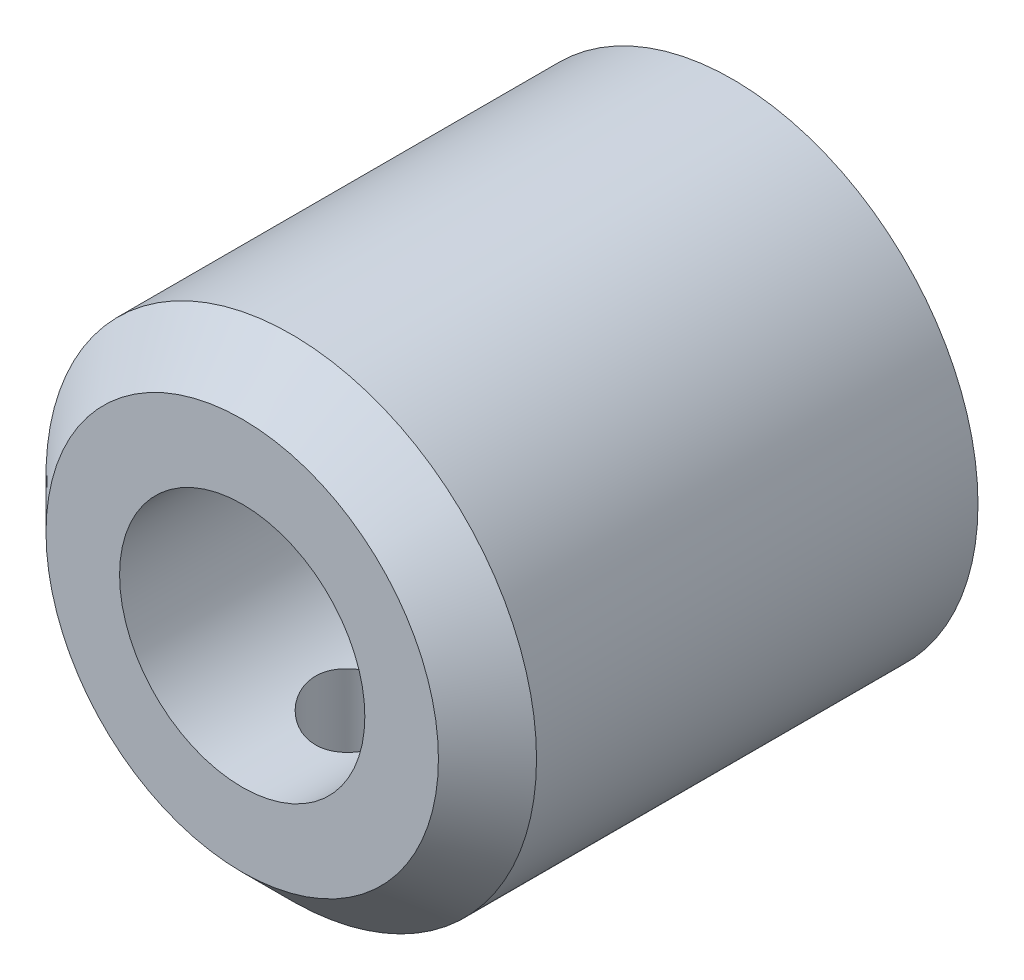
SolidWorks part; units mm, degrees
ref_plane "Front" through (0, 0, 0) normal (0, 0, 1) x (1, 0, 0)
ref_plane "Top" through (0, 0, 0) normal (0, 1, 0) x (1, 0, 0)
ref_plane "Right" through (0, 0, 0) normal (1, 0, 0) x (0, 0, -1)
sketch "Sketch1" plane through (0, 0, 0) normal (0, 0, 1) x (1, 0, 0)
  circle A0 centre (0, 0) radius 12.7
  dimension "D1" = 25.4
extrude "Boss-Extrude1" add sketch "Sketch1" along normal blind 25.4
sketch "Sketch2" plane through (0, 0, 25.4) normal (0, 0, 1) x (1, 0, 0)
  circle A0 centre (0, 0) radius 2.5527
  dimension "D1" = 5.1054
extrude "Cut-Extrude1" cut sketch "Sketch2" against normal through all
sketch "Sketch3" plane through (0, 0, 25.4) normal (0, 0, 1) x (1, 0, 0)
  circle A0 centre (0, 0) radius 6.35
  dimension "D1" = 12.7
extrude "Cut-Extrude2" cut sketch "Sketch3" against normal offset from surface (19.05 mm away) 6.35 up to face at (2.5527, 0, 0)
chamfer "Chamfer1" distance 2.54 angle 45 1 edges at (12.7, 0, 25.4)
sketch "Sketch4" plane through (0, 0, 0) normal (0, 1, 0) x (1, 0, 0)
  line L0 (0, 0) -> (0, -25.6506) construction
  line L1 (12.7, 0) -> (-12.7, 0) construction
  circle A0 centre (0, -19.05) radius 2.5527
  point P5 (0, -16.8628)
  dimension "D1" = 5.1054
  dimension "D2" = 19.05
extrude "Cut-Extrude3" cut sketch "Sketch4" against normal blind 19.05
